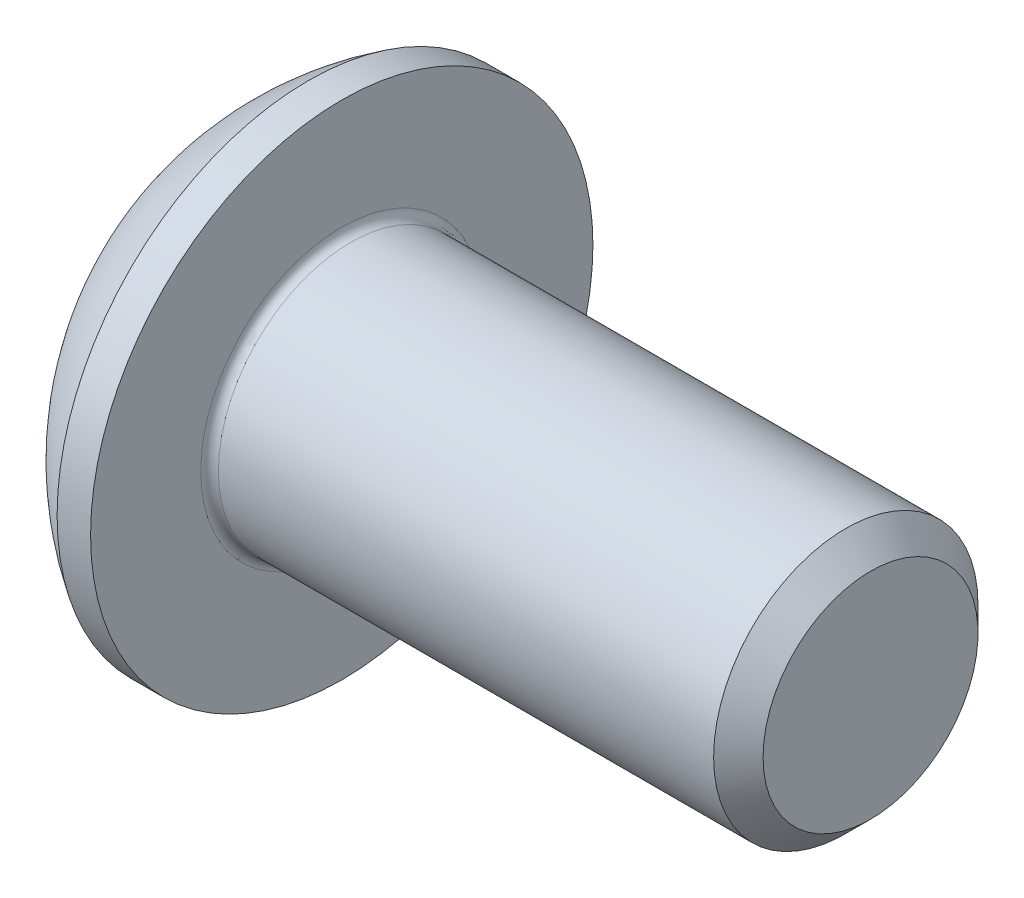
SolidWorks part; units mm, degrees
ref_plane "Plane1" through (0, 0, 0) normal (0, 0, 1) x (1, 0, 0)
ref_plane "Plane2" through (0, 0, 0) normal (0, 1, 0) x (1, 0, 0)
ref_plane "Plane3" through (0, 0, 0) normal (1, 0, 0) x (0, 0, -1)
sketch "BodySke" plane through (0, 0, 0) normal (0, 0, 1) x (1, 0, 0)
  line L0 (7.65, 0) -> (7.65, 1.2195)
  line L1 (7.3695, 1.5) -> (1.65, 1.5)
  line L2 (1.65, 1.5) -> (1.65, 2.85)
  line L3 (1.65, 2.85) -> (1.27, 2.85)
  line L4 (0, 0) -> (101.6, 0) construction
  line L5 (1.65, -2.85) -> (1.27, -2.85) construction
  line L6 (55.6768, -1.5) -> (1.65, -1.5) construction
  line L7 (7.65, 0) -> (0, 0)
  line L8 (0, 1.425) -> (0, -1.425) construction
  line L9 (0, 0) -> (0, 1.425)
  line L10 (7.65, 1.2195) -> (7.3695, 1.5)
  line L11 (7.65, -1.2195) -> (7.3695, -1.5) construction
  line L12 (2.15, 9.525) -> (2.15, -1.5) construction
  line L13 (1.65, 9.525) -> (1.65, -1.5) construction
  arc A1 (0, 1.425) -> (1.27, 2.85) centre (3.0334, 0) cw
  dimension "Diameter" = 3
  dimension "Length" = 6
  dimension "Head_dia" = 5.7
  dimension "D1" = 2.85
  dimension "Head_ht" = 1.65
  dimension "Head_side_ht" = 0.38
  dimension "Minor_dia" = 2.439
  dimension "Body_ch_ang" = 45
  dimension "Advance" = 0.5
  dimension "Thread_nom" = 6
revolve "BaseBody" add sketch "BodySke" angle 360 about L4
cosmetic thread "ThreadCosmetic" [suppressed] parameters "Thread_length"=5, "Thread_minor"=2.439
fillet "Fillet1" radius 0.1 1 edges at (1.65, 0, 1.5)
sketch "Sketch2" plane through (0, 0, 0) normal (0, 0, 1) x (1, 0, 0)
  line L0 (0, 1) -> (1.04, 1)
  line L1 (1.04, 1) -> (1.6174, 0)
  line L3 (1.6174, 0) -> (0, 0)
  line L4 (0, 0) -> (0, 1)
  line L5 (0, -1) -> (1.04, -1) construction
  line L6 (0, 0) -> (47.625, 0) construction
  dimension "D2" = 60
  dimension "PreBroach_depth" = 1.04
  dimension "PreBroach_dia" = 2
revolve "PreBroach" cut sketch "Sketch2" angle 360 about L6
sketch "Sketch3" plane through (0, 0, 0) normal (1, 0, 0) x (0, 0, -1)
  line L0 (-1, -0.5774) -> (-1, 0.5774)
  line L1 (-1, 0.5774) -> (0, 1.1547)
  line L2 (0, 1.1547) -> (1, 0.5774)
  line L3 (1, 0.5774) -> (1, -0.5774)
  line L4 (1, -0.5774) -> (0, -1.1547)
  line L5 (0, -1.1547) -> (-1, -0.5774)
  dimension "Hex_size" = 2
  dimension "D3" = 2
  dimension "D1" = 1
  dimension "D2" = 1
extrude "Hex" cut sketch "Sketch3" along normal blind 1.04
sketch "ThdSchSke" plane through (0, 0, 0) normal (0, 0, 1) x (1, 0, 0)
  line L0 (2.65, -1.2195) -> (2.4536, -1.5)
  line L1 (2.65, -1.2195) -> (2.8464, -1.5)
  line L2 (2.8464, -1.5) -> (2.8464, -1.875)
  line L3 (-3.175, 0) -> (5.1513, 0) construction
  line L5 (2.8464, -1.875) -> (2.4536, -1.875)
  line L6 (2.4536, -1.875) -> (2.4536, -1.5)
  dimension "Diameter" = 3
  dimension "Thread_minor" = 2.439
  dimension "SideAngle" = 55
  dimension "VeeAngle" = 70
  dimension "Overcut" = 3.75
  dimension "Start" = 2.65
revolve "ThreadSchematic" [suppressed] cut sketch "ThdSchSke" angle 360 about L3
pattern_linear "ThdSchPat" [suppressed]
equation "\"D1@BodySke\" = \"Head_dia@BodySke\" * .5"
equation "\"Thread_minor@ThreadCosmetic\" = \"Minor_dia@BodySke\""
equation "\"D1@Sketch3\" = \"Hex_size@Sketch3\" / 2"
equation "\"D2@Sketch3\" = \"D1@Sketch3\""
equation "\"D3@Sketch3\" = \"Hex_size@Sketch3\""
equation "\"Thread_length@ThreadCosmetic\" = ((sgn( (\"Length@BodySke\" - \"Advance@BodySke\" * 2.0) - \"Thread_nom@BodySke\" )-1)*( (\"Length@BodySke\" - \"Advance@BodySke\" * 2.0) - \"Thread_nom@BodySke\" ))/-2+ \"Thread_nom@BodySke\""
equation "\"Thread_minor@ThdSchSke\" = \"Minor_dia@BodySke\""
equation "\"Diameter@ThdSchSke\" = \"Diameter@BodySke\""
equation "\"Overcut@ThdSchSke\" = \"Diameter@BodySke\" * 1.25"
equation "\"Start@ThdSchSke\" = \"Head_ht@BodySke\" + \"Length@BodySke\" - \"Thread_length@ThreadCosmetic\"  '---Non-countersunk---"
equation "\"Num_threads@ThdSchPat\" = int( \"Thread_length@ThreadCosmetic\" / \"Advance@BodySke\" + 0.999 )  + 1"
equation "\"Advance@ThdSchPat\" = \"Thread_length@ThreadCosmetic\" /  (\"Num_threads@ThdSchPat\" - 1) 'relax it"
equation "\"Num_threads@ThdSchPat\" = \"Num_threads@ThdSchPat\" - sgn( \"Num_threads@ThdSchPat\" - 1) '---chamfered tips only---"
